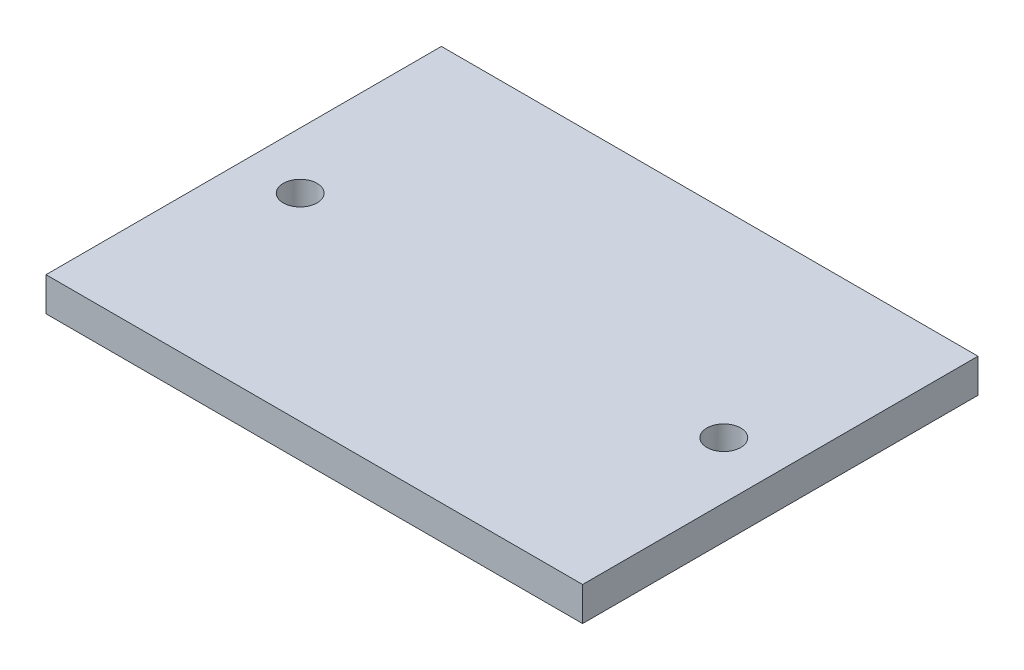
SolidWorks part; units mm, degrees
ref_plane "Front Plane" through (0, 0, 0) normal (0, 0, 1) x (1, 0, 0)
ref_plane "Top Plane" through (0, 0, 0) normal (0, 1, 0) x (1, 0, 0)
ref_plane "Right Plane" through (0, 0, 0) normal (1, 0, 0) x (0, 0, -1)
sketch "Sketch2" plane through (0, 0, 0) normal (0, 1, 0) x (1, 0, 0)
  line L1 (0, 0) -> (47.5, 0)
  line L2 (0, 0) -> (0, 35)
  line L3 (0, 35) -> (47.5, 35)
  line L4 (47.5, 0) -> (47.5, 35)
  dimension "D1" = 47.5
  dimension "D2" = 35
extrude "Boss-Extrude1" add sketch "Sketch2" along normal blind 3
hole_wizard "Ø3.0mm Dowel Hole1" positions "Sketch3" profile "Sketch4" hole size "Ø3.0" standard "ANSI Metric" end condition up to next
sketch "Sketch3" plane through (0, 3, 0) normal (0, 1, 0) x (1, 0, 0)
  line L0 (0, 17.5) -> (47.5, 17.5) construction
  line L1 (0, 35) -> (0, 0) construction
  line L2 (47.5, 0) -> (47.5, 35) construction
  line L4 (47.5, 35) -> (0, 35) construction
  point P0 (5, 17.5)
  point P2 (42.5, 17.5)
  dimension "D1" = 17.5
  dimension "D2" = 5
  dimension "D3" = 5
sketch "Sketch4" plane through (5, 3, -17.5) normal (1, 0, 0) x (0, 0, 1)
  line L0 (0, 0) -> (0, 3)
  line L1 (0, 3) -> (1.5, 3)
  line L2 (1.5, 3) -> (1.5, 0)
  line L5 (1.5, 0) -> (0, 0)
  line L11 (0, -6.35) -> (0, 107.95) construction
  dimension "Thru Hole Dia." = 3
  dimension "Thru Hole Depth" = 3
